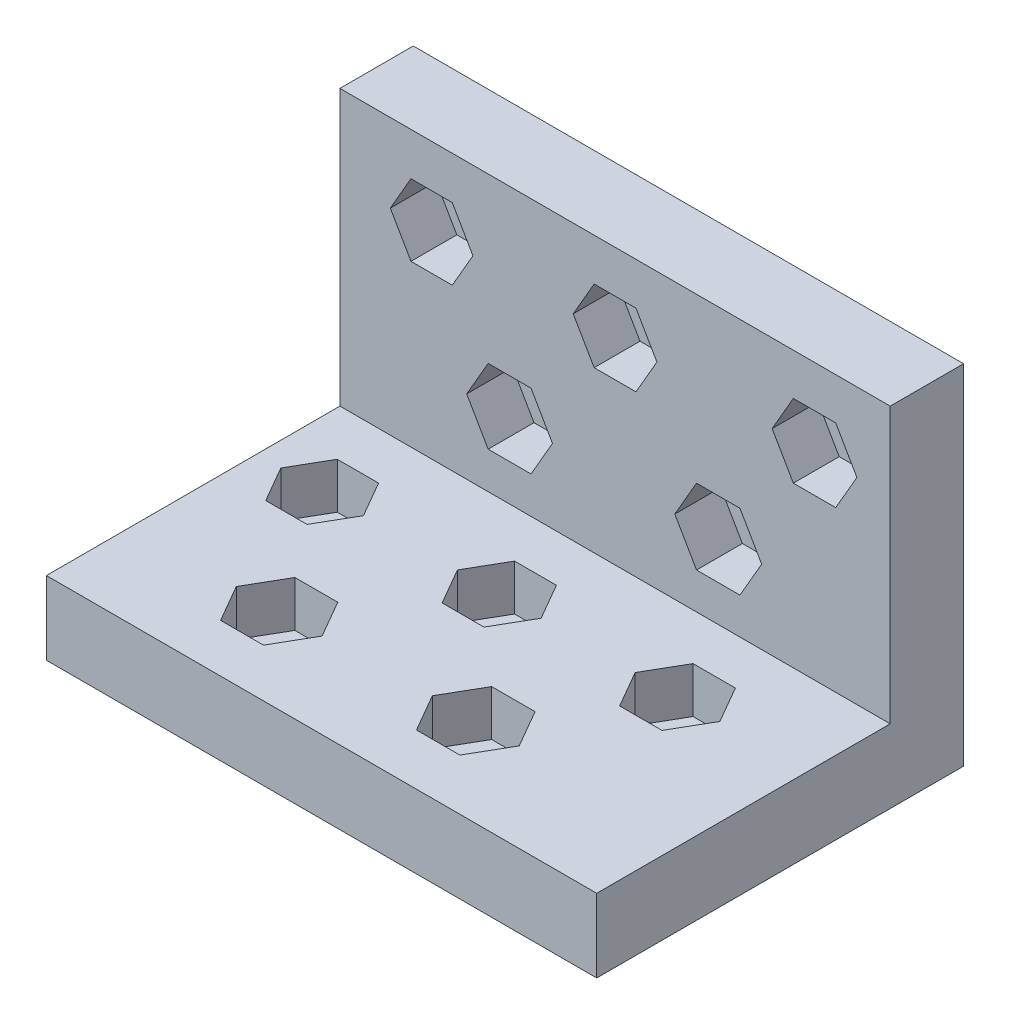
SolidWorks part; units mm, degrees
ref_plane "Front Plane" through (0, 0, 0) normal (0, 0, 1) x (1, 0, 0)
ref_plane "Top Plane" through (0, 0, 0) normal (0, 1, 0) x (1, 0, 0)
ref_plane "Right Plane" through (0, 0, 0) normal (1, 0, 0) x (0, 0, -1)
sketch "Sketch1" plane through (0, 0, 0) normal (0, 1, 0) x (1, 0, 0)
  line L1 (-15, 10) -> (15, 10)
  line L2 (-15, 10) -> (-15, -10)
  line L3 (-15, -10) -> (15, -10)
  line L4 (15, 10) -> (15, -10)
  line L5 (-15, 10) -> (15, -10) construction
  line L6 (-15, -10) -> (15, 10) construction
  point P0 (0, 0)
  dimension "D1" = 30
  dimension "D2" = 20
extrude "Boss-Extrude1" add sketch "Sketch1" along normal blind 4
sketch "Sketch2" plane through (0, 4, 0) normal (0, 1, 0) x (1, 0, 0)
  line L0 (15, -10) -> (15, 10) construction
  line L1 (-15, 10) -> (15, 10)
  line L2 (-15, 10) -> (-15, 6)
  line L3 (-15, 6) -> (15, 6)
  line L4 (15, 10) -> (15, 6)
  dimension "D1" = 4
extrude "Boss-Extrude2" add sketch "Sketch2" along normal blind 15
sketch "Sketch3" plane through (0, 0, -6) normal (0, 0, 1) x (1, 0, 0)
  line L0 (-15, 4) -> (15, 4) construction
  line L1 (-8.8742, 12.7712) -> (-7.7483, 14.7212)
  line L2 (-7.7483, 14.7212) -> (-8.8742, 16.6712)
  line L3 (-8.8742, 16.6712) -> (-11.1258, 16.6712)
  line L4 (-11.1258, 16.6712) -> (-12.2517, 14.7212)
  line L5 (-12.2517, 14.7212) -> (-11.1258, 12.7712)
  line L6 (-11.1258, 12.7712) -> (-8.8742, 12.7712)
  line L31 (-15, 19) -> (-15, 4) construction
  line L51 (1.1403, 12.743) -> (2.2805, 14.718)
  line L52 (2.2805, 14.718) -> (1.1403, 16.693)
  line L53 (1.1403, 16.693) -> (-1.1403, 16.693)
  line L54 (-1.1403, 16.693) -> (-2.2805, 14.718)
  line L55 (-2.2805, 14.718) -> (-1.1403, 12.743)
  line L56 (-1.1403, 12.743) -> (1.1403, 12.743)
  line L57 (12.0282, 12.7212) -> (13.1829, 14.7212)
  line L58 (13.1829, 14.7212) -> (12.0282, 16.7212)
  line L59 (12.0282, 16.7212) -> (9.7188, 16.7212)
  line L60 (9.7188, 16.7212) -> (8.5641, 14.7212)
  line L61 (8.5641, 14.7212) -> (9.7188, 12.7212)
  line L62 (9.7188, 12.7212) -> (12.0282, 12.7212)
  line L63 (-4.5801, 6.0064) -> (-3.411, 8.0314)
  line L64 (-3.411, 8.0314) -> (-4.5801, 10.0564)
  line L65 (-4.5801, 10.0564) -> (-6.9184, 10.0564)
  line L66 (-6.9184, 10.0564) -> (-8.0875, 8.0314)
  line L67 (-8.0875, 8.0314) -> (-6.9184, 6.0064)
  line L68 (-6.9184, 6.0064) -> (-4.5801, 6.0064)
  line L69 (6.8078, 5.9814) -> (7.9914, 8.0314)
  line L70 (7.9914, 8.0314) -> (6.8078, 10.0814)
  line L71 (6.8078, 10.0814) -> (4.4407, 10.0814)
  line L72 (4.4407, 10.0814) -> (3.2571, 8.0314)
  line L73 (3.2571, 8.0314) -> (4.4407, 5.9814)
  line L74 (4.4407, 5.9814) -> (6.8078, 5.9814)
  circle A0 centre (-10, 14.7212) radius 1.95 construction
  circle A1 centre (0, 14.718) radius 1.975 construction
  circle A2 centre (10.8735, 14.7212) radius 2 construction
  circle A3 centre (-5.7492, 8.0314) radius 2.025 construction
  circle A4 centre (5.6242, 8.0314) radius 2.05 construction
  dimension "D4" = 4
  dimension "D2" = 5
  dimension "D3" = 3.95
  dimension "D1" = 3.9
  dimension "D5" = 4.05
  dimension "D6" = 4.1
extrude "Cut-Extrude1" cut sketch "Sketch3" against normal blind 2.5
sketch "Sketch4" plane through (0, 0, -8.5) normal (0, 0, 1) x (1, 0, 0)
  circle A0 centre (-10, 14.7212) radius 1
  circle A1 centre (0, 14.718) radius 1
  circle A2 centre (10.8735, 14.7212) radius 1
  circle A3 centre (5.6242, 8.0314) radius 1
  circle A4 centre (-5.7492, 8.0314) radius 1
  dimension "D1" = 2
extrude "Cut-Extrude2" cut sketch "Sketch4" against normal through all both and the other way through all
sketch "Sketch5" plane through (0, 4, 0) normal (0, 1, 0) x (1, 0, 0)
  line L1 (-10.3101, -0.4814) -> (-9.1843, 1.4686)
  line L2 (-9.1843, 1.4686) -> (-10.3101, 3.4186)
  line L3 (-10.3101, 3.4186) -> (-12.5618, 3.4186)
  line L4 (-12.5618, 3.4186) -> (-13.6876, 1.4686)
  line L5 (-13.6876, 1.4686) -> (-12.5618, -0.4814)
  line L6 (-12.5618, -0.4814) -> (-10.3101, -0.4814)
  line L7 (-0.6407, -0.5064) -> (0.4995, 1.4686)
  line L8 (0.4995, 1.4686) -> (-0.6407, 3.4436)
  line L9 (-0.6407, 3.4436) -> (-2.9213, 3.4436)
  line L10 (-2.9213, 3.4436) -> (-4.0615, 1.4686)
  line L11 (-4.0615, 1.4686) -> (-2.9213, -0.5064)
  line L12 (-2.9213, -0.5064) -> (-0.6407, -0.5064)
  line L13 (9.0911, -0.5314) -> (10.2458, 1.4686)
  line L14 (10.2458, 1.4686) -> (9.0911, 3.4686)
  line L15 (9.0911, 3.4686) -> (6.7817, 3.4686)
  line L16 (6.7817, 3.4686) -> (5.627, 1.4686)
  line L17 (5.627, 1.4686) -> (6.7817, -0.5314)
  line L18 (6.7817, -0.5314) -> (9.0911, -0.5314)
  line L19 (-5.7987, -7.368) -> (-4.6295, -5.343)
  line L20 (-4.6295, -5.343) -> (-5.7987, -3.318)
  line L21 (-5.7987, -3.318) -> (-8.1369, -3.318)
  line L22 (-8.1369, -3.318) -> (-9.3061, -5.343)
  line L23 (-9.3061, -5.343) -> (-8.1369, -7.368)
  line L24 (-8.1369, -7.368) -> (-5.7987, -7.368)
  line L25 (4.7456, -7.2056) -> (5.9292, -5.1556)
  line L26 (5.9292, -5.1556) -> (4.7456, -3.1056)
  line L27 (4.7456, -3.1056) -> (2.3785, -3.1056)
  line L28 (2.3785, -3.1056) -> (1.1949, -5.1556)
  line L29 (1.1949, -5.1556) -> (2.3785, -7.2056)
  line L30 (2.3785, -7.2056) -> (4.7456, -7.2056)
  circle A0 centre (-11.436, 1.4686) radius 1.95 construction
  circle A1 centre (-1.781, 1.4686) radius 1.975 construction
  circle A2 centre (7.9364, 1.4686) radius 2 construction
  circle A3 centre (-6.9678, -5.343) radius 2.025 construction
  circle A4 centre (3.562, -5.1556) radius 2.05 construction
  dimension "D1" = 3.9
  dimension "D2" = 3.95
  dimension "D3" = 4
  dimension "D4" = 4.05
  dimension "D5" = 4.1
extrude "Cut-Extrude3" cut sketch "Sketch5" against normal blind 2.5 and the other way through all
sketch "Sketch6" plane through (0, 1.5, 0) normal (0, 1, 0) x (1, 0, 0)
  circle A0 centre (-11.436, 1.4686) radius 1
  circle A1 centre (-1.781, 1.4686) radius 1
  circle A2 centre (7.9364, 1.4686) radius 1
  circle A3 centre (3.562, -5.1556) radius 1
  circle A4 centre (-6.9678, -5.343) radius 1
  dimension "D1" = 2
extrude "Cut-Extrude4" cut sketch "Sketch6" against normal through all both and the other way through all
